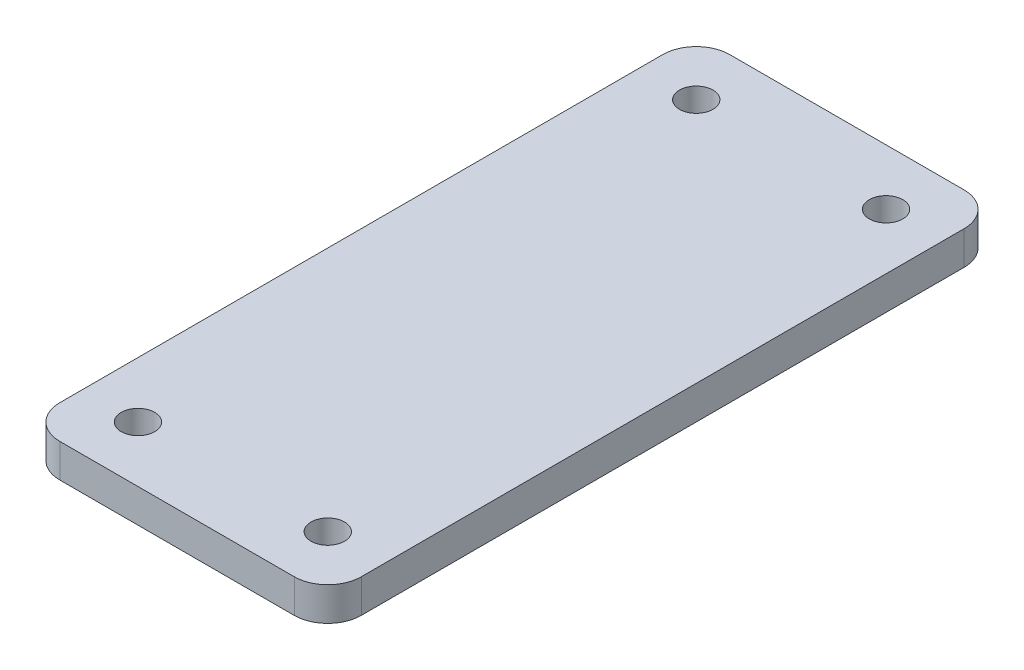
SolidWorks part; units mm, degrees
ref_plane "Front Plane" through (0, 0, 0) normal (0, 0, 1) x (1, 0, 0)
ref_plane "Top Plane" through (0, 0, 0) normal (0, 1, 0) x (1, 0, 0)
ref_plane "Right Plane" through (0, 0, 0) normal (1, 0, 0) x (0, 0, -1)
sketch "Sketch3" plane through (0, 0, 0) normal (0, 1, 0) x (1, 0, 0)
  line L1 (13.5, 30) -> (-13.5, 30)
  line L2 (13.5, 30) -> (13.5, -30)
  line L3 (13.5, -30) -> (-13.5, -30)
  line L4 (-13.5, 30) -> (-13.5, -30)
  line L5 (13.5, 30) -> (-13.5, -30) construction
  line L6 (13.5, -30) -> (-13.5, 30) construction
  point P0 (0, 0)
  dimension "D1" = 60
  dimension "D2" = 27
extrude "Boss-Extrude1" add sketch "Sketch3" along normal blind 3
sketch "Sketch4" plane through (0, 3, 0) normal (0, 1, 0) x (1, 0, 0)
  line L0 (13.5, -30) -> (13.5, 30) construction
  line L4 (-13.5, -30) -> (13.5, -30) construction
  line L5 (13.5, 30) -> (-13.5, 30) construction
  line L8 (-13.5, 30) -> (-13.5, -30) construction
  circle A0 centre (-8.5, 25) radius 1.5
  circle A1 centre (8.5, 25) radius 1.5
  circle A2 centre (8.5, -25) radius 1.5
  circle A3 centre (-8.5, -25) radius 1.5
  point P0 (8.5, 25)
  point P1 (8.5, -25)
  point P2 (-8.5, -25)
  point P3 (-8.5, 25)
  dimension "D1" = 5
  dimension "D2" = 5
  dimension "D3" = 5
  dimension "D4" = 5
  dimension "D5" = 5
  dimension "D6" = 5
  dimension "D7" = 5
  dimension "D8" = 5
extrude "Cut-Extrude1" cut sketch "Sketch4" against normal blind 3
fillet "Fillet2" radius 3 1 edges at (-13.5, 1.5, 30)
fillet "Fillet3" radius 3 3 edges at (-13.5, 1.5, -30) (13.5, 1.5, -30) (13.5, 1.5, 30)
